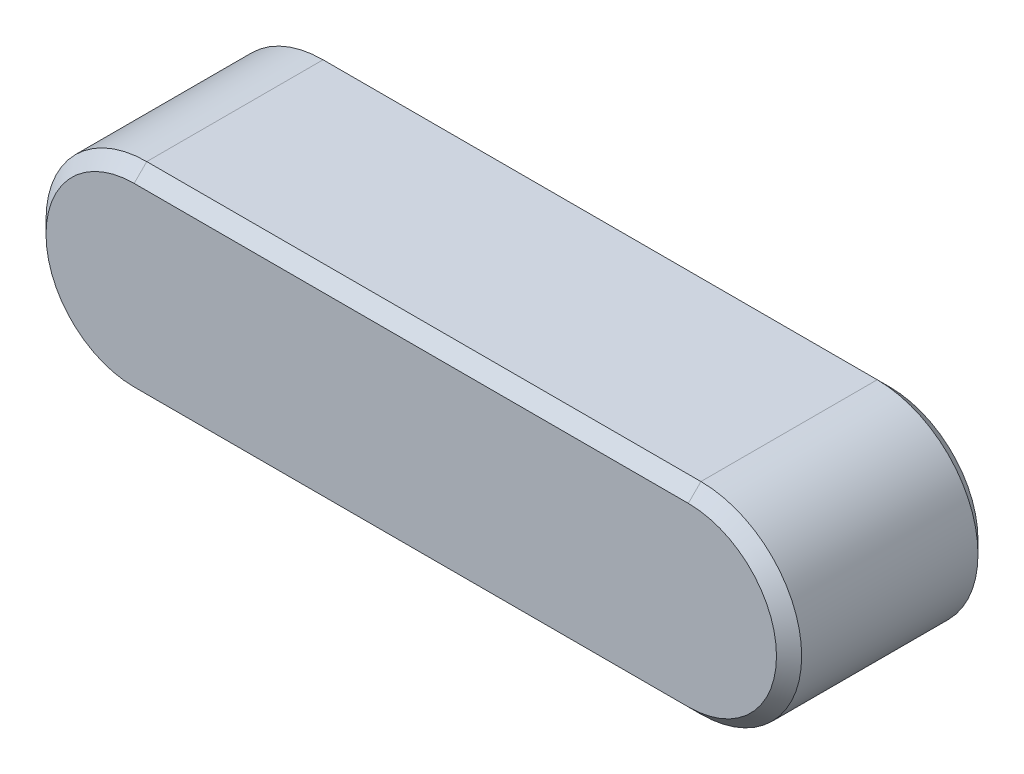
SolidWorks part; units mm, degrees
ref_plane "Přední rovina" through (0, 0, 0) normal (0, 0, 1) x (1, 0, 0)
ref_plane "Horní rovina" through (0, 0, 0) normal (0, 1, 0) x (1, 0, 0)
ref_plane "Pravá rovina" through (0, 0, 0) normal (1, 0, 0) x (0, 0, -1)
sketch "Skica1" plane through (0, 0, 0) normal (0, 0, 1) x (1, 0, 0)
  line L0 (0, 0) -> (22, 0) construction
  line L1 (0, 4) -> (22, 4)
  line L2 (0, -4) -> (22, -4)
  arc A0 (0, 4) -> (0, -4) centre (0, 0) ccw
  arc A1 (22, -4) -> (22, 4) centre (22, 0) ccw
  point P3 (11, 0)
  dimension "D1" = 8
  dimension "D2" = 22
extrude "Přidat vysunutím1" add sketch "Skica1" along normal blind 8
chamfer "Zkosení1" distance 0.5 angle 45 8 edges at (-4, 0, 0) (11, -4, 0) (11, 4, 0) (26, 0, 0) (11, 4, 8) (-4, 0, 8) (26, 0, 8) (11, -4, 8)
